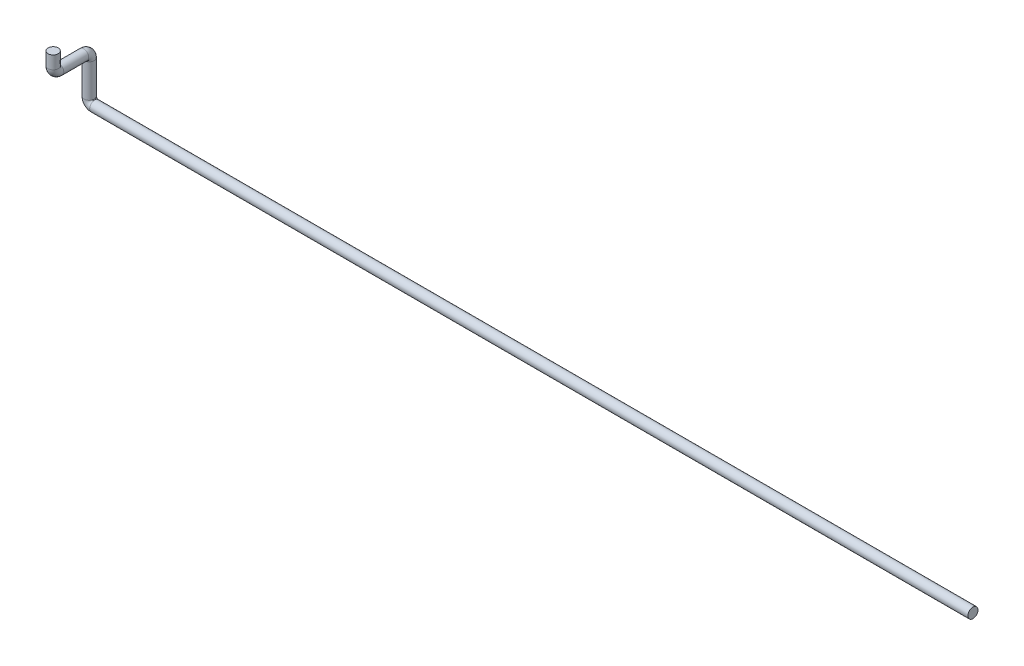
SolidWorks part; units mm, degrees
ref_plane "Alzado" through (0, 0, 0) normal (0, 0, 1) x (1, 0, 0)
ref_plane "Planta" through (0, 0, 0) normal (0, 1, 0) x (1, 0, 0)
ref_plane "Vista lateral" through (0, 0, 0) normal (1, 0, 0) x (0, 0, -1)
sketch3d "Croquis3D1"
  line L0 (0, 0, 0) -> (-2374, 0, 0)
  line L1 (-2389, 15, 0) -> (-2389, 105, 0)
  line L2 (-2389, 120, 15) -> (-2389, 120, 82.5)
  line L3 (-2389, 135, 97.5) -> (-2389, 170, 97.5)
  arc A0 (-2389, 105, 0) -> (-2389, 120, 15) centre (-2389, 105, 15) ccw
  arc A1 (-2374, 0, 0) -> (-2389, 15, 0) centre (-2374, 15, 0) ccw
  arc A2 (-2389, 120, 82.5) -> (-2389, 135, 97.5) centre (-2389, 135, 82.5) ccw
  point P8 (-2389, 120, 0)
  point P9 (-2374, 105, 15)
  point P12 (-2389, 0, 0)
  point P13 (-2374, 15, -15)
  point P16 (-2389, 120, 97.5)
  point P17 (-2404, 135, 82.5)
  dimension "D5" = 15
  dimension "D1" = 2389
  dimension "D2" = 120
  dimension "D3" = 97.5
  dimension "D4" = 50
sketch "Croquis1" plane through (0, 0, 0) normal (1, 0, 0) x (0, 0, -1)
  circle A0 centre (0, 0) radius 13.7
  dimension "D1" = 27.4
sweep "Barrer1" add profiles "Croquis1" path "Croquis3D1"
